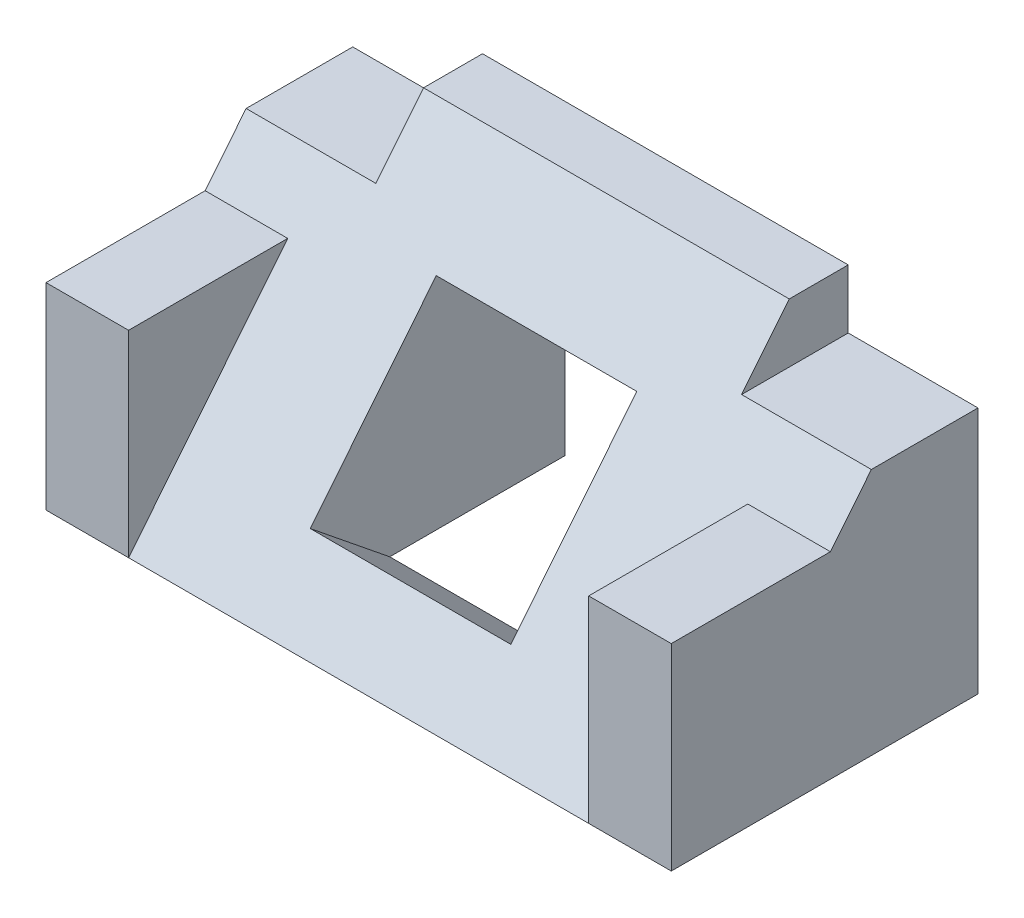
SolidWorks part; units mm, degrees
ref_plane "Front Plane" through (0, 0, 0) normal (0, 0, 1) x (1, 0, 0)
ref_plane "Top Plane" through (0, 0, 0) normal (0, 1, 0) x (1, 0, 0)
ref_plane "Right Plane" through (0, 0, 0) normal (1, 0, 0) x (0, 0, -1)
sketch "Sketch2" plane through (0, 0, 0) normal (1, 0, 0) x (0, 0, -1)
  line L1 (0, 0) -> (26, 0)
  line L2 (0, 0) -> (0, 26)
  line L3 (0, 26) -> (26, 26)
  line L4 (26, 0) -> (26, 26)
  dimension "D1" = 26
extrude "Boss-Extrude1" add sketch "Sketch2" along normal blind 53
sketch "Sketch3" plane through (53, 0, 0) normal (1, 0, 0) x (0, 0, -1)
  line L0 (0, 0) -> (21, 26)
  line L1 (26, 26) -> (0, 26) construction
  dimension "D1" = 5
extrude "Cut-Extrude2" cut sketch "Sketch3" against normal through all and the other way through all
sketch "Sketch4" plane through (0, 0, -26) normal (0, 0, -1) x (-1, 0, 0)
  line L0 (-26.5, 26) -> (-26.5, 13.1816) construction
  line L1 (-53, 26) -> (0, 26) construction
  line L2 (0, 21) -> (-11, 21)
  line L3 (-53, 26) -> (-42, 26)
  line L4 (-53, 26) -> (-53, 21)
  line L5 (-53, 21) -> (-42, 21)
  line L6 (-42, 26) -> (-42, 21)
  line L7 (-11, 26) -> (-11, 21)
  line L8 (0, 26) -> (-11, 26)
  line L9 (0, 26) -> (0, 21)
  dimension "D1" = 5
  dimension "D2" = 11
extrude "Cut-Extrude3" cut sketch "Sketch4" against normal through all
sketch "Sketch5" plane through (0, 0, 0) normal (0, 0.6283, 0.7779) x (1, 0, 0)
  line L0 (26.5, 0) -> (26.5, 39.6154) construction
  line L1 (53, 0) -> (0, 0) construction
  line L2 (0, 13.4972) -> (26.5, 13.4972) construction
  line L3 (0, 0) -> (0, 26.9943) construction
  line L4 (53, 0) -> (53, 26.9943) construction
  line L9 (35, 7) -> (18, 7)
  line L10 (35, 7) -> (35, 24)
  line L11 (35, 24) -> (18, 24)
  line L12 (18, 7) -> (18, 24)
  line L13 (35, 7) -> (18, 24) construction
  line L14 (35, 24) -> (18, 7) construction
  point P8 (26.5, 15.5)
  dimension "D1" = 17
  dimension "D2" = 17
  dimension "D3" = 7
  dimension "D4" = 18
extrude "Cut-Extrude4" cut sketch "Sketch5" against normal through all
sketch "Sketch6" plane through (53, 0, 0) normal (1, 0, 0) x (0, 0, -1)
  line L0 (0, 0) -> (0, 16.7)
  line L1 (0, 16.7) -> (13.4885, 16.7)
  line L2 (0, 0) -> (16.9615, 21) construction
  line L3 (13.4885, 16.7) -> (0, 0)
  dimension "D1" = 16.7
extrude "Boss-Extrude3" add sketch "Sketch6" against normal blind 7
sketch "Sketch8" plane through (0, 0, 0) normal (-1, 0, 0) x (0, 0, 1)
  line L0 (0, 0) -> (0, 16.7)
  line L1 (0, 16.7) -> (-13.4885, 16.7)
  line L2 (0, 0) -> (-13.4885, 16.7)
extrude "Boss-Extrude4" add sketch "Sketch8" against normal blind 7
